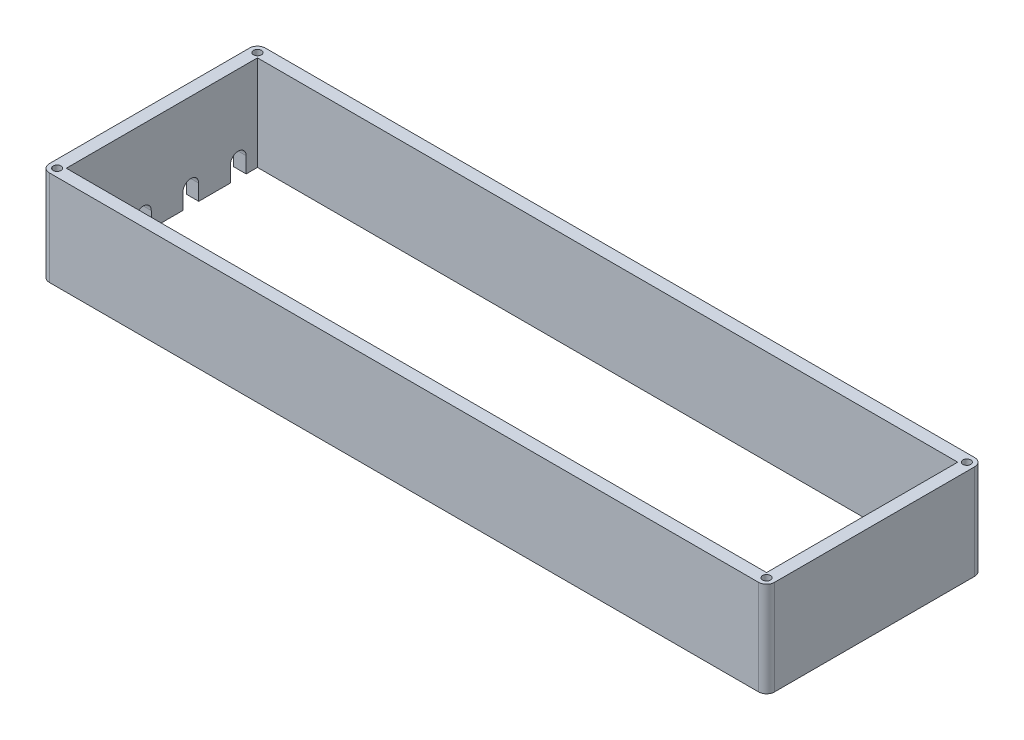
SolidWorks part; units mm, degrees
material "ABS PC"
ref_plane "Front" through (0, 0, 0) normal (0, 0, 1) x (1, 0, 0)
ref_plane "Top" through (0, 0, 0) normal (0, 1, 0) x (1, 0, 0)
ref_plane "Right" through (0, 0, 0) normal (1, 0, 0) x (0, 0, -1)
sketch "Sketch1" plane through (0, 0, 0) normal (0, 1, 0) x (1, 0, 0)
  line L0 (-517.9531, -293.3337) -> (-517.9531, -139.8517)
  line L1 (-517.9531, -139.8517) -> (-1080.1131, -139.8517)
  line L2 (-1080.1131, -139.8517) -> (-1080.1131, -293.3337)
  line L3 (-1080.1131, -293.3337) -> (-517.9531, -293.3337)
  line L4 (-514.3031, -129.8517) -> (-1083.7631, -129.8517)
  line L5 (-1090.1131, -136.2017) -> (-1090.1131, -296.9837)
  line L6 (-1083.7631, -303.3337) -> (-514.3031, -303.3337)
  line L7 (-507.9531, -296.9837) -> (-507.9531, -136.2017)
  line L24 (-514.3031, -129.8517) -> (-1083.7631, -129.8517)
  line L25 (-1090.1131, -136.2017) -> (-1090.1131, -296.9837)
  line L26 (-1083.7631, -303.3337) -> (-514.3031, -303.3337)
  line L27 (-507.9531, -296.9837) -> (-507.9531, -136.2017)
  circle A4 centre (-1083.7631, -136.2017) radius 3.175 construction
  circle A5 centre (-1083.7631, -296.9837) radius 3.175 construction
  circle A6 centre (-514.3031, -136.2017) radius 3.175 construction
  circle A7 centre (-514.3031, -296.9837) radius 3.175 construction
  arc A16 (-1083.7631, -129.8517) -> (-1090.1131, -136.2017) centre (-1083.7631, -136.2017) ccw
  arc A17 (-1090.1131, -296.9837) -> (-1083.7631, -303.3337) centre (-1083.7631, -296.9837) ccw
  arc A18 (-514.3031, -303.3337) -> (-507.9531, -296.9837) centre (-514.3031, -296.9837) ccw
  arc A19 (-507.9531, -136.2017) -> (-514.3031, -129.8517) centre (-514.3031, -136.2017) ccw
  arc A30 (-1083.7631, -129.8517) -> (-1090.1131, -136.2017) centre (-1083.7631, -136.2017) ccw
  arc A31 (-1090.1131, -296.9837) -> (-1083.7631, -303.3337) centre (-1083.7631, -296.9837) ccw
  arc A32 (-514.3031, -303.3337) -> (-507.9531, -296.9837) centre (-514.3031, -296.9837) ccw
  arc A33 (-507.9531, -136.2017) -> (-514.3031, -129.8517) centre (-514.3031, -136.2017) ccw
  circle A34 centre (-1083.7631, -136.2017) radius 3.175
  circle A35 centre (-1083.7631, -296.9837) radius 3.175
  circle A36 centre (-514.3031, -136.2017) radius 3.175
  circle A37 centre (-514.3031, -296.9837) radius 3.175
  arc A38 (-517.9531, -139.8517) -> (-517.9531, -139.8517) centre (-517.9531, -139.8517) ccw
  arc A39 (-1080.1131, -139.8517) -> (-1080.1131, -139.8517) centre (-1080.1131, -139.8517) ccw
  arc A40 (-1080.1131, -293.3337) -> (-1080.1131, -293.3337) centre (-1080.1131, -293.3337) ccw
  arc A41 (-517.9531, -293.3337) -> (-517.9531, -293.3337) centre (-517.9531, -293.3337) ccw
  point P4 (0, 0)
  point P25 (0, 0)
  dimension "D1" = 0
  dimension "D2" = 10
extrude "Boss-Extrude1" add sketch "Sketch1" along normal blind 76.2
sketch "Sketch3" plane through (-1090.1131, 0, 0) normal (-1, 0, 0) x (0, 0, 1)
  line L0 (161.6017, 0) -> (148.9017, 0)
  line L1 (136.2017, 0) -> (296.9837, 0) construction
  line L2 (148.9017, 0) -> (148.9017, 12.7)
  line L4 (161.6017, 12.7) -> (161.6017, 0)
  line L5 (199.7017, 0) -> (187.0017, 0)
  line L6 (187.0017, 0) -> (187.0017, 12.7)
  line L7 (199.7017, 12.7) -> (199.7017, 0)
  line L8 (237.8017, 0) -> (225.1017, 0)
  line L9 (225.1017, 0) -> (225.1017, 12.7)
  line L10 (237.8017, 12.7) -> (237.8017, 0)
  line L11 (275.9017, 0) -> (263.2017, 0)
  line L12 (263.2017, 0) -> (263.2017, 12.7)
  line L13 (275.9017, 12.7) -> (275.9017, 0)
  arc A0 (161.6017, 12.7) -> (148.9017, 12.7) centre (155.2517, 12.7) ccw
  arc A1 (199.7017, 12.7) -> (187.0017, 12.7) centre (193.3517, 12.7) ccw
  arc A2 (237.8017, 12.7) -> (225.1017, 12.7) centre (231.4517, 12.7) ccw
  arc A3 (275.9017, 12.7) -> (263.2017, 12.7) centre (269.5517, 12.7) ccw
  dimension "D1" = 12.7
  dimension "D2" = 12.7
  dimension "D3" = 12.7
  dimension "D4" = 4
extrude "Cut-Extrude1" cut sketch "Sketch3" against normal up to next
